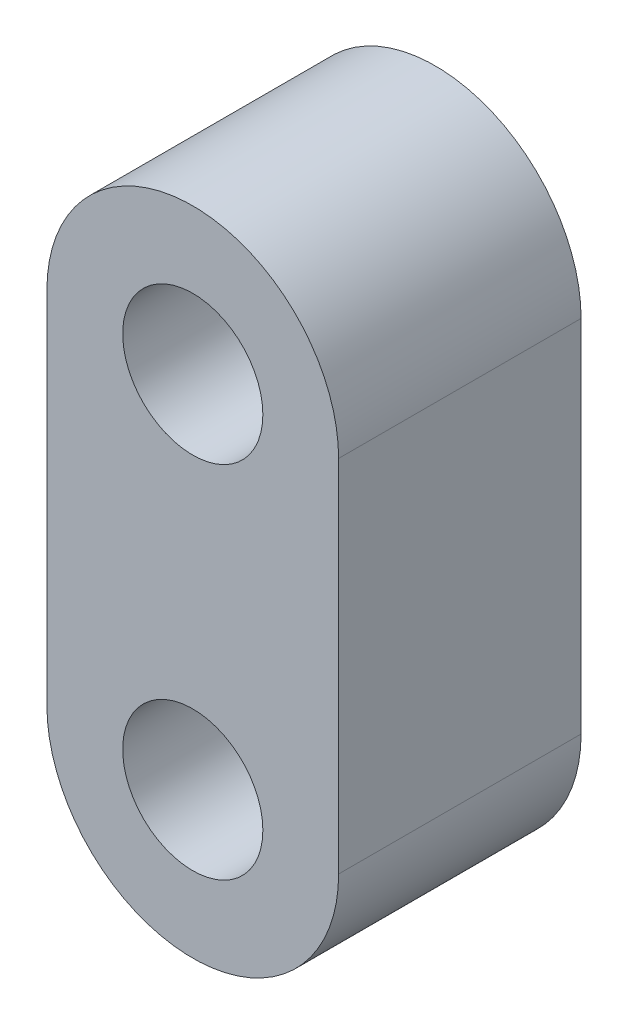
SolidWorks part; units mm, degrees
ref_plane "Alzado" through (0, 0, 0) normal (0, 0, 1) x (1, 0, 0)
ref_plane "Planta" through (0, 0, 0) normal (0, 1, 0) x (1, 0, 0)
ref_plane "Vista lateral" through (0, 0, 0) normal (1, 0, 0) x (0, 0, -1)
sketch "Croquis1" plane through (0, 0, 0) normal (0, 0, 1) x (1, 0, 0)
  line L0 (0, 0) -> (0, -9.5) construction
  line L1 (3.85, 0) -> (3.85, -9.5)
  line L2 (-3.85, 0) -> (-3.85, -9.5)
  circle A0 centre (0, 0) radius 1.85
  circle A1 centre (0, -9.5) radius 1.85
  arc A2 (3.85, 0) -> (-3.85, 0) centre (0, 0) ccw
  arc A3 (-3.85, -9.5) -> (3.85, -9.5) centre (0, -9.5) ccw
  point P5 (0, -4.75)
  dimension "D1" = 9.5
  dimension "D2" = 3.7
  dimension "D3" = 3.7
  dimension "D4" = 2
extrude "Saliente-Extruir1" add sketch "Croquis1" along normal blind 6.4
